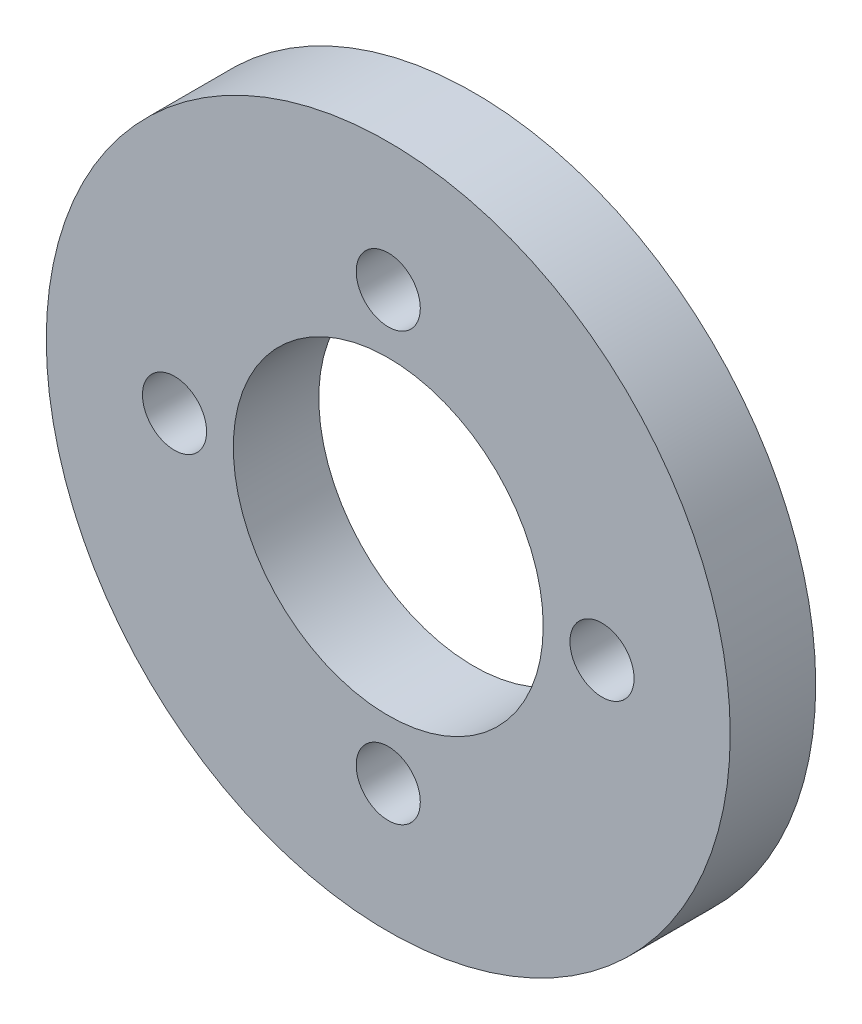
SolidWorks part; units mm, degrees
material "Acrylic (Medium-high impact)"
ref_plane "Front Plane" through (0, 0, 0) normal (0, 0, 1) x (1, 0, 0)
ref_plane "Top Plane" through (0, 0, 0) normal (0, 1, 0) x (1, 0, 0)
ref_plane "Right Plane" through (0, 0, 0) normal (1, 0, 0) x (0, 0, -1)
sketch "Sketch1" plane through (0, 0, 0) normal (0, 0, 1) x (1, 0, 0)
  circle A0 centre (0, 0) radius 16
  circle A1 centre (0, 0) radius 7.25
  circle A2 centre (0, 0) radius 10 construction
  circle A3 centre (0, 10) radius 1.5
  circle A4 centre (10, 0) radius 1.5
  circle A5 centre (0, -10) radius 1.5
  circle A6 centre (-10, 0) radius 1.5
  point P12 (0, 0)
  dimension "D1" = 14.5
  dimension "D2" = 32
  dimension "D3" = 3
  dimension "D4" = 20
extrude "Boss-Extrude1" add sketch "Sketch1" along normal blind 4
